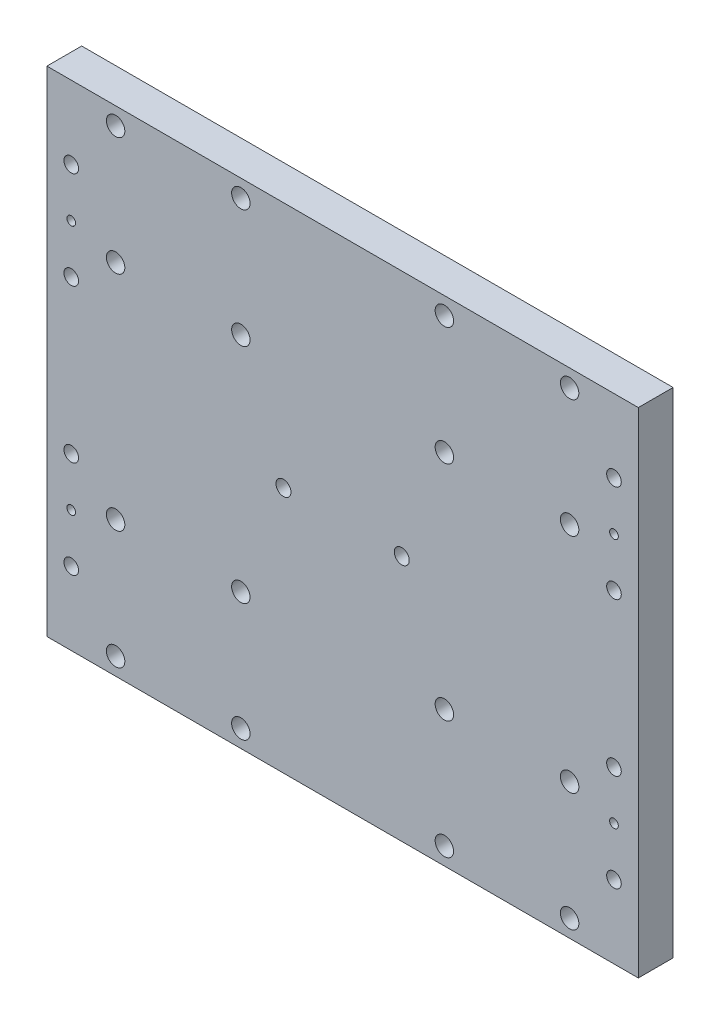
SolidWorks part; units mm, degrees
ref_plane "Front Plane" through (0, 0, 0) normal (0, 0, 1) x (1, 0, 0)
ref_plane "Top Plane" through (0, 0, 0) normal (0, 1, 0) x (1, 0, 0)
ref_plane "Right Plane" through (0, 0, 0) normal (1, 0, 0) x (0, 0, -1)
sketch "Sketch1" plane through (0, 0, 0) normal (0, 0, 1) x (1, 0, 0)
  line L1 (85, -71) -> (-85, -71)
  line L2 (85, -71) -> (85, 71)
  line L3 (85, 71) -> (-85, 71)
  line L4 (-85, -71) -> (-85, 71)
  line L5 (85, -71) -> (-85, 71) construction
  line L6 (85, 71) -> (-85, -71) construction
  point P0 (0, 0)
  dimension "D1" = 170
  dimension "D2" = 142
extrude "Boss-Extrude1" add sketch "Sketch1" along normal mid plane 10
hole_wizard "M5 Clearance Hole1" positions "Sketch8" profile "Sketch7" hole size "M5" standard "ANSI Metric" end condition through all
sketch "Sketch8" plane through (0, 0, 5) normal (0, 0, 1) x (1, 0, 0)
  line L1 (-29.25, 32) -> (-65.25, 32) construction
  line L2 (-29.25, 32) -> (-29.25, 66) construction
  line L3 (-29.25, 66) -> (-65.25, 66) construction
  line L4 (-65.25, 32) -> (-65.25, 66) construction
  line L5 (-29.25, 32) -> (-65.25, 66) construction
  line L6 (-29.25, 66) -> (-65.25, 32) construction
  line L9 (85, 71) -> (-85, 71) construction
  line L10 (-85, 71) -> (-85, -71) construction
  point P0 (-65.25, 66)
  point P2 (-29.25, 66)
  point P4 (-29.25, 32)
  point P6 (-65.25, 32)
  dimension "D1" = 5
  dimension "D2" = 19.75
  dimension "D3" = 34
  dimension "D4" = 36
sketch "Sketch7" plane through (-65.25, 66, 5) normal (1, 0, 0) x (0, -1, 0)
  line L0 (0, 0) -> (0, 10)
  line L1 (0, 10) -> (2.65, 10)
  line L2 (2.65, 10) -> (2.65, 0)
  line L5 (2.65, 0) -> (0, 0)
  line L11 (0, -6.35) -> (0, 107.95) construction
  dimension "Thru Hole Dia." = 5.3
  dimension "Thru Hole Depth" = 10
mirror "Mirror2" about plane through (0, 0, 0) normal (0, 1, 0) of "M5 Clearance Hole1"
mirror "Mirror3" about plane through (0, 0, 0) normal (1, 0, 0) of "Mirror2", "M5 Clearance Hole1"
hole_wizard "M4 Clearance Hole1" positions "Sketch10" profile "Sketch9" hole size "M4" standard "ANSI Metric" end condition through all
sketch "Sketch10" plane through (0, 0, 5) normal (0, 0, 1) x (1, 0, 0)
  line L0 (-1000, 0) -> (49000, 0) construction
  point P0 (-17, 0)
  point P2 (17, 0)
  dimension "D1" = 17
  dimension "D2" = 17
sketch "Sketch9" plane through (-17, 0, 5) normal (1, 0, 0) x (0, -1, 0)
  line L0 (0, 0) -> (0, 10)
  line L1 (0, 10) -> (2.15, 10)
  line L2 (2.15, 10) -> (2.15, 0)
  line L5 (2.15, 0) -> (0, 0)
  line L11 (0, -6.35) -> (0, 107.95) construction
  dimension "Thru Hole Dia." = 4.3
  dimension "Thru Hole Depth" = 10
hole_wizard "M5x0.8 Tapped Hole1" positions "Sketch12" profile "Sketch11" tap size "M5x0.8" standard "ANSI Metric"
sketch "Sketch12" plane through (0, 0, 5) normal (0, 0, 1) x (1, 0, 0)
  line L0 (-78, -1023.3996) -> (-78, 48976.6004) construction
  line L1 (-85, 71) -> (-85, -71) construction
  line L2 (-1000, 0) -> (49000, 0) construction
  point P0 (-78, 50)
  point P2 (-78, 22)
  dimension "D1" = 7
  dimension "D2" = 22
  dimension "D3" = 50
sketch "Sketch11" plane through (-78, 50, 5) normal (1, 0, 0) x (0, -1, 0)
  line L0 (0, 0) -> (0, 15.2618)
  line L1 (0, 15.2618) -> (2.1, 14)
  line L2 (2.1, 14) -> (2.1, 0)
  line L5 (2.1, 0) -> (0, 0)
  line L10 (0, 15.2618) -> (-2.1, 14) construction
  line L11 (0, -6.35) -> (0, 107.95) construction
  dimension "Tap Drill Dia." = 4.2
  dimension "Tap Drill Depth" = 14
  dimension "Drill Angle" = 118
cosmetic thread "Hole Thread1" parameters "D1"=10, "D2"=5
cosmetic thread "Hole Thread2" parameters "D1"=10, "D2"=5
sketch "Sketch6" plane through (0, 0, 5) normal (0, 0, 1) x (1, 0, 0)
  line L0 (-78, -1002.1032) -> (-78, 48997.8968) construction
  line L1 (78, -1010.3548) -> (78, 48989.6452) construction
  line L2 (-85, 71) -> (-85, -71) construction
  line L3 (85, -71) -> (85, 71) construction
  line L6 (-1000, 0) -> (49000, 0) construction
  circle A1 centre (-78, 36) radius 1.25
  dimension "D4" = 2.5
  dimension "D1" = 7
  dimension "D2" = 7
  dimension "D10" = 36
extrude "Cut-Extrude5" cut sketch "Sketch6" against normal through all
mirror "Mirror1" about plane through (0, 0, 0) normal (1, 0, 0) of "M5x0.8 Tapped Hole1", "Cut-Extrude5"
mirror "Mirror4" about plane through (0, 0, 0) normal (0, 1, 0) of "Mirror1", "M5x0.8 Tapped Hole1", "Cut-Extrude5"
